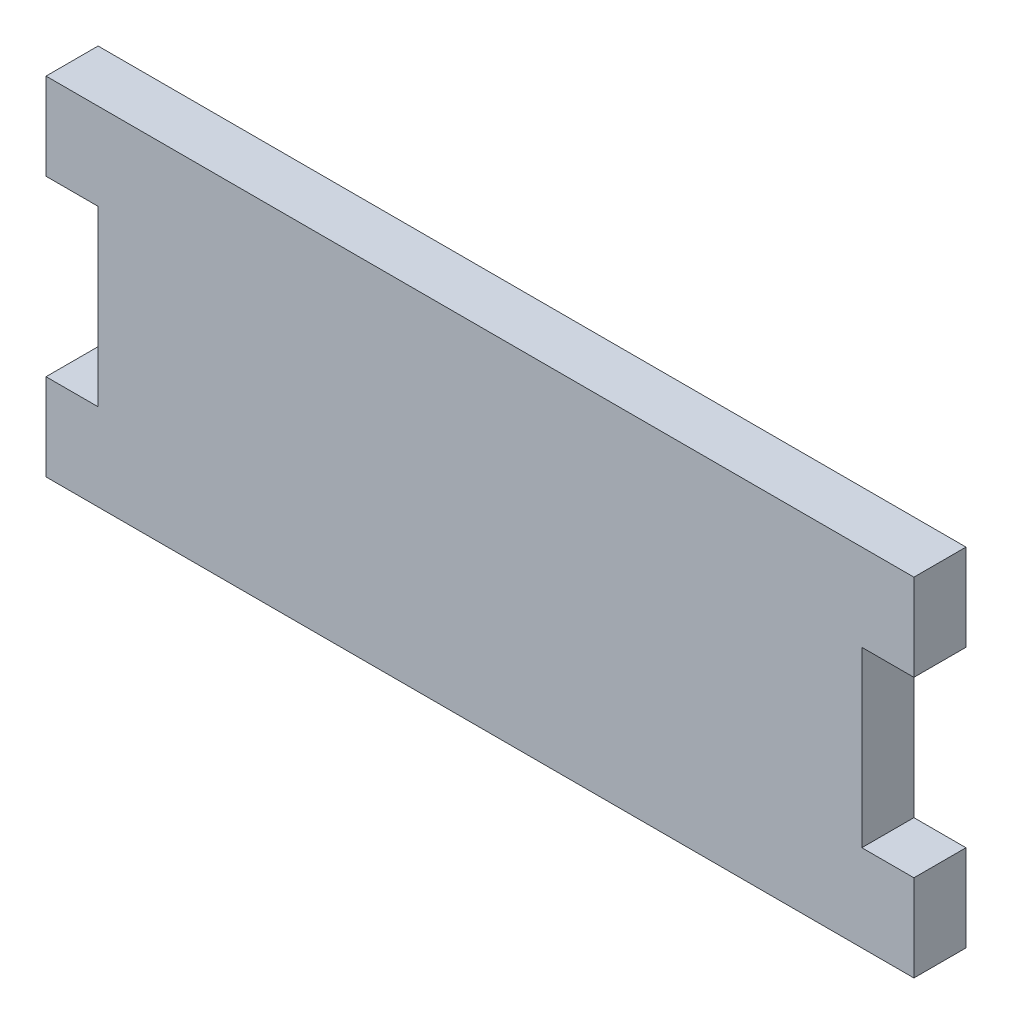
SolidWorks part; units mm, degrees
ref_plane "Alzado" through (0, 0, 0) normal (0, 0, 1) x (1, 0, 0)
ref_plane "Planta" through (0, 0, 0) normal (0, 1, 0) x (1, 0, 0)
ref_plane "Vista lateral" through (0, 0, 0) normal (1, 0, 0) x (0, 0, -1)
sketch "Model" plane through (0, 0, 0) normal (0, 0, 1) x (1, 0, 0)
  line L0 (46.2616, 3.5648) -> (-3.7384, 3.5648)
  line L1 (46.2616, 23.5648) -> (-3.7384, 23.5648)
  line L2 (-3.7384, 18.5648) -> (-3.7384, 23.5648)
  line L3 (46.2616, 18.5648) -> (46.2616, 23.5648)
  line L4 (-3.7384, 18.5648) -> (-0.7384, 18.5648)
  line L5 (-0.7384, 18.5648) -> (-0.7384, 8.5648)
  line L6 (-0.7384, 8.5648) -> (-3.7384, 8.5648)
  line L7 (-3.7384, 8.5648) -> (-3.7384, 3.5648)
  line L8 (46.2616, 18.5648) -> (43.2616, 18.5648)
  line L9 (43.2616, 18.5648) -> (43.2616, 8.5648)
  line L10 (43.2616, 8.5648) -> (46.2616, 8.5648)
  line L11 (46.2616, 8.5648) -> (46.2616, 3.5648)
extrude "Saliente-Extruir1" add sketch "Model" along normal blind 3 contours L5 L6 L7 L0 L11 L10 L9 L8 L3 L1 L2 L4
